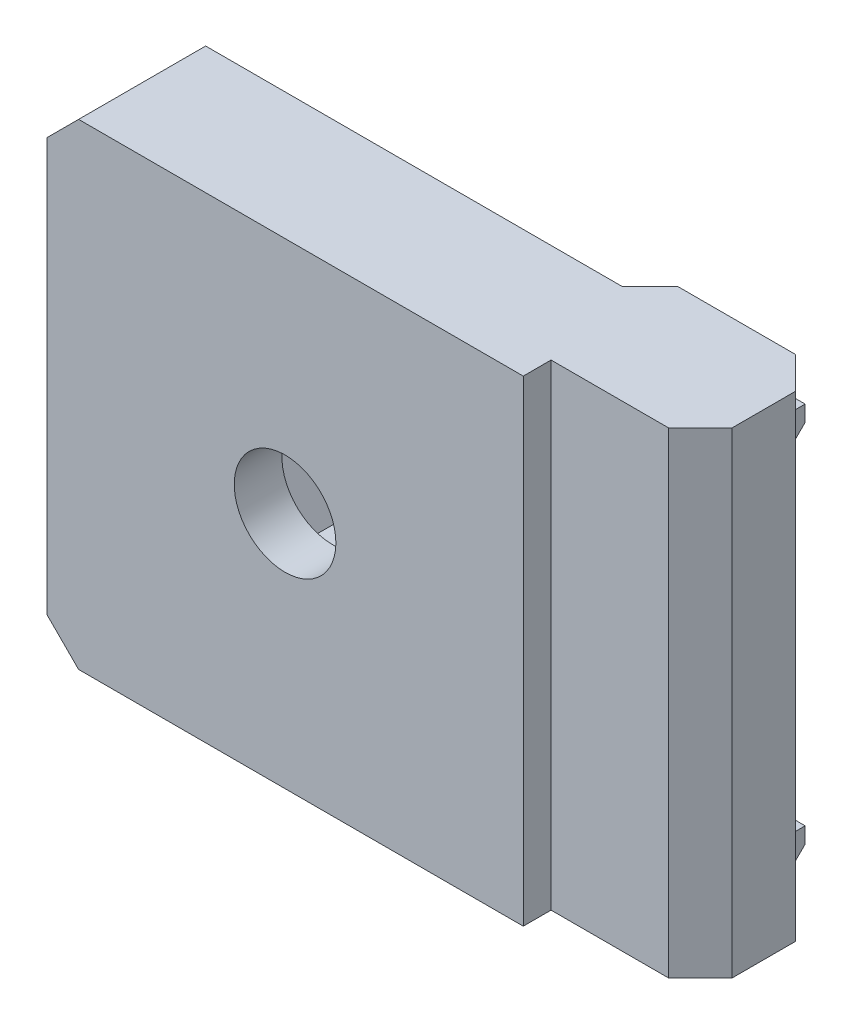
SolidWorks part; units mm, degrees
ref_plane "Alzado" through (0, 0, 0) normal (0, 0, 1) x (1, 0, 0)
ref_plane "Planta" through (0, 0, 0) normal (0, 1, 0) x (1, 0, 0)
ref_plane "Vista lateral" through (0, 0, 0) normal (1, 0, 0) x (0, 0, -1)
sketch "Croquis1" plane through (0, 0, 0) normal (0, 1, 0) x (1, 0, 0)
  line L0 (0, 0) -> (-30, 0)
  line L1 (-30, 0) -> (-30, 8)
  line L2 (-30, 8) -> (-1.75, 8)
  line L3 (-1.75, 8) -> (0, 9.75)
  line L4 (0, 9.75) -> (9.4, 9.75)
  line L5 (9.4, 9.75) -> (9.4, 1.75)
  line L6 (9.4, 1.75) -> (0, 1.75)
  line L7 (0, 1.75) -> (0, 0)
  line L8 (-15, 18.5318) -> (-15, -3.9407) construction
  point P10 (-30, 6.726)
  dimension "D1" = 1.75
  dimension "D2" = 30
  dimension "D3" = 8
  dimension "D4" = 9.4
  dimension "D5" = 15
  dimension "D6" = 45
extrude "Saliente-Extruir1" add sketch "Croquis1" along normal mid plane 30
sketch "Croquis2" plane through (0, 0, 0) normal (0, 0, 1) x (1, 0, 0)
  line L0 (0, 0) -> (-50000, 0) construction
  circle A0 centre (-15, 0) radius 3.2
  dimension "D2" = 6.4
  dimension "D1" = 15
extrude "Cortar-Extruir1" cut sketch "Croquis2" against normal through all
sketch "Croquis3" plane through (0, 0, 0) normal (0, 0, 1) x (1, 0, 0)
  line L1 (-9.2265, 0) -> (-12.1132, 5)
  line L2 (-12.1132, 5) -> (-17.8868, 5)
  line L3 (-17.8868, 5) -> (-20.7735, 0)
  line L4 (-20.7735, 0) -> (-17.8868, -5)
  line L5 (-17.8868, -5) -> (-12.1132, -5)
  line L6 (-12.1132, -5) -> (-9.2265, 0)
  circle A0 centre (-15, 0) radius 5 construction
  dimension "D1" = 10
extrude "Cortar-Extruir2" cut sketch "Croquis3" against normal through all from offset 3 offset against normal yes
chamfer "Chaflán1" distance 2 angle 45 4 edges at (9.4, 0, -1.75) (9.4, 0, -9.75) (-30, -15, -4) (-30, 15, -4)
sketch "Croquis5" plane through (0, 0, 0) normal (1, 0, 0) x (0, 0, -1)
  line L0 (0, 0) -> (50000, 0) construction
  line L1 (9.75, 12) -> (10.35, 12)
  line L2 (9.75, 15) -> (9.75, -15) construction
  line L3 (10.35, 12) -> (10.35, 11)
  line L4 (10.35, 11) -> (9.75, 10.4)
  line L5 (9.75, 10.4) -> (9.75, 12)
  line L6 (7.75, 15) -> (9.75, 15) construction
  line L7 (9.75, -11) -> (10.35, -11)
  line L8 (10.35, -11) -> (10.35, -12)
  line L9 (10.35, -12) -> (9.75, -12.6)
  line L10 (9.75, -12.6) -> (9.75, -11)
  line L11 (9.75, -15) -> (7.75, -15) construction
  point P15 (9.75, -8.5969)
  dimension "D1" = 0.6
  dimension "D2" = 1
  dimension "D3" = 1.6
  dimension "D4" = 3
  dimension "D5" = 0.6
  dimension "D6" = 1
  dimension "D7" = 1.6
  dimension "D8" = 3
extrude "Saliente-Extruir3" add sketch "Croquis5" along normal up to vertex (7.4 mm away) up to point (7.4, 15, -9.75)
